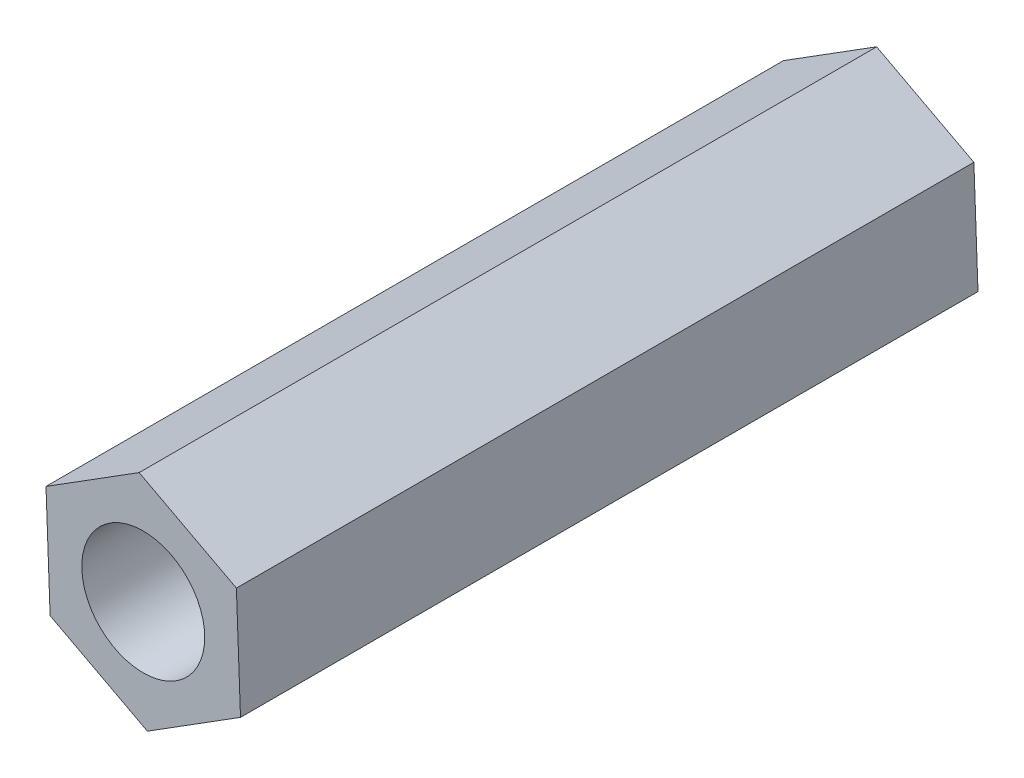
SolidWorks part; units mm, degrees
ref_plane "前视基准面" through (0, 0, 0) normal (0, 0, 1) x (1, 0, 0)
ref_plane "上视基准面" through (0, 0, 0) normal (0, 1, 0) x (1, 0, 0)
ref_plane "右视基准面" through (0, 0, 0) normal (1, 0, 0) x (0, 0, -1)
sketch "草图1" plane through (0, 0, 0) normal (0, 0, 1) x (1, 0, 0)
  line L1 (2.2732, 1.4283) -> (-0.1003, 2.6828)
  line L2 (-0.1003, 2.6828) -> (-2.3735, 1.2545)
  line L3 (-2.3735, 1.2545) -> (-2.2732, -1.4283)
  line L4 (-2.2732, -1.4283) -> (0.1003, -2.6828)
  line L5 (0.1003, -2.6828) -> (2.3735, -1.2545)
  line L6 (2.3735, -1.2545) -> (2.2732, 1.4283)
  circle A0 centre (0, 0) radius 2.325 construction
  circle A1 centre (0, 0) radius 1.5
extrude "凸台-拉伸1" add sketch "草图1" along normal blind 18
